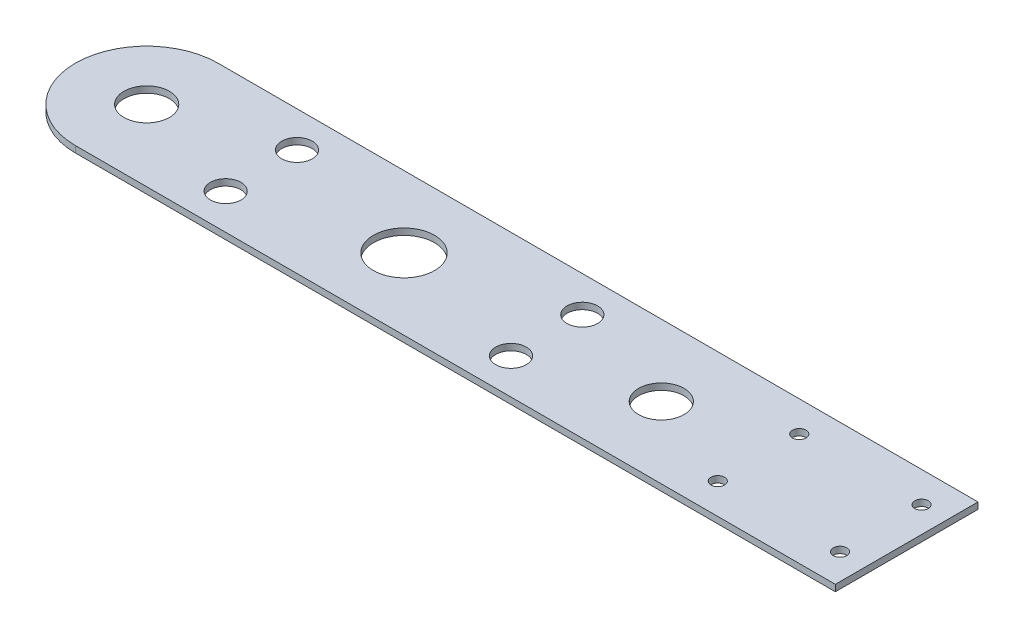
SolidWorks part; units mm, degrees
ref_plane "Front Plane" through (0, 0, 0) normal (0, 0, 1) x (1, 0, 0)
ref_plane "Top Plane" through (0, 0, 0) normal (0, 1, 0) x (1, 0, 0)
ref_plane "Right Plane" through (0, 0, 0) normal (1, 0, 0) x (0, 0, -1)
sketch "Sketch1" plane through (0, 0, 0) normal (0, 1, 0) x (1, 0, 0)
  line L0 (126.2582, 0) -> (-126.2582, 0)
  line L1 (-126.2582, 35) -> (126.2582, 35)
  line L3 (-126.2582, -35) -> (126.2582, -35)
  line L4 (-70, 35) -> (-70, 0) construction
  line L5 (-70, 0) -> (-70, -35) construction
  line L6 (70, 35) -> (70, 0) construction
  line L7 (70, 0) -> (70, -35) construction
  line L8 (161.2582, 35) -> (161.2582, -35) construction
  line L9 (161.2582, 35) -> (126.2582, 35)
  line L10 (161.2582, -35) -> (126.2582, -35)
  line L11 (161.2582, 35) -> (246.6582, 35)
  line L12 (246.6582, 35) -> (246.6582, -35)
  line L13 (246.6582, -35) -> (161.2582, -35)
  line L14 (246.6582, 0) -> (161.2582, 0) construction
  line L15 (202.1966, 20) -> (202.1966, -20) construction
  line L16 (246.6582, -20) -> (161.2582, -20) construction
  line L17 (246.6582, 20) -> (161.2582, 20) construction
  circle A0 centre (-126.2582, 0) radius 35
  circle A2 centre (-126.2582, 0) radius 11.15
  circle A3 centre (126.2582, 0) radius 11.15
  circle A4 centre (0, 0) radius 15
  circle A5 centre (-70, -17.5) radius 7.5
  circle A6 centre (-70, 17.5) radius 7.5
  circle A7 centre (70, 17.5) radius 7.5
  circle A8 centre (70, -17.5) radius 7.5
  circle A11 centre (233.9582, -20) radius 3.325
  circle A12 centre (233.9582, 20) radius 3.325
  circle A13 centre (173.9582, 20) radius 3.325
  circle A14 centre (173.9582, -20) radius 3.325
  point P4 (0, 0)
  point P31 (-161.2582, 0)
  point P32 (161.2582, 0)
  point P38 (202.1966, 0)
  dimension "D1" = 22.3
  dimension "D2" = 30
  dimension "D3" = 70
  dimension "D4" = 15
  dimension "D10" = 60
  dimension "D9" = 6.65
  dimension "D5" = 70
  dimension "D6" = 70
  dimension "D7" = 322.5164
  dimension "D8" = 40
  dimension "D11" = 60
  dimension "D12" = 12.7
  dimension "D13" = 12.7
  dimension "D14" = 12.7
extrude "Boss-Extrude1" add sketch "Sketch1" along normal blind 3.175
